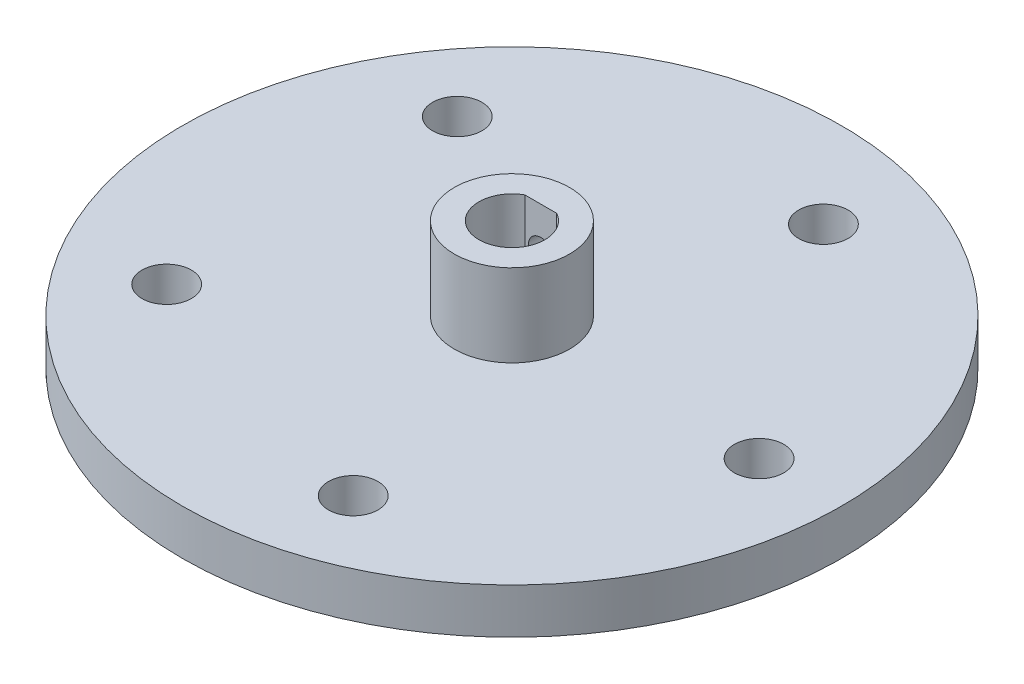
SolidWorks part; units mm, degrees
material "Malleable Cast Iron"
ref_plane "Front Plane" through (0, 0, 0) normal (0, 0, 1) x (1, 0, 0)
ref_plane "Top Plane" through (0, 0, 0) normal (0, 1, 0) x (1, 0, 0)
ref_plane "Right Plane" through (0, 0, 0) normal (1, 0, 0) x (0, 0, -1)
sketch "Sketch1" plane through (0, 0, 0) normal (0, 1, 0) x (1, 0, 0)
  circle A0 centre (0, 0) radius 40
  dimension "D1" = 80
extrude "Boss-Extrude1" add sketch "Sketch1" along normal blind 5.5
sketch "Sketch2" plane through (0, 5.5, 0) normal (0, 1, 0) x (1, 0, 0)
  circle A0 centre (30, 0) radius 3
  dimension "D1" = 30
extrude "Cut-Extrude1" cut sketch "Sketch2" against normal through all
pattern_circular "CirPattern1" count 5 over 360 about axis through (0, 0, 0) along (0, 1, 0) of "Cut-Extrude1"
sketch "Sketch3" plane through (0, 5.5, 0) normal (0, 1, 0) x (1, 0, 0)
  circle A0 centre (0, 0) radius 7
  dimension "D1" = 14
extrude "Boss-Extrude2" add sketch "Sketch3" along normal blind 10
sketch "Sketch7" plane through (0, 15.5, 0) normal (0, 1, 0) x (1, 0, 0)
  line L0 (2.8588, 3.5) -> (-1.9365, 3.5)
  circle A0 centre (0, 0) radius 4
  point P6 (0.4611, 3.5)
  dimension "D1" = 8
  dimension "D2" = 3.5
extrude "Cut-Extrude2" cut sketch "Sketch7" against normal blind 20 contours L0 A0
sketch "Sketch8" plane through (0, 0, 0) normal (0, 0, 1) x (1, 0, 0)
  line L0 (7, 15.5) -> (-7, 15.5) construction
  line L1 (7, 5.5) -> (7, 15.5) construction
  circle A0 centre (0, 10.5) radius 1.5
  dimension "D1" = 3
  dimension "D2" = 5
  dimension "D3" = 7
extrude "Cut-Extrude3" cut sketch "Sketch8" against normal blind 10
